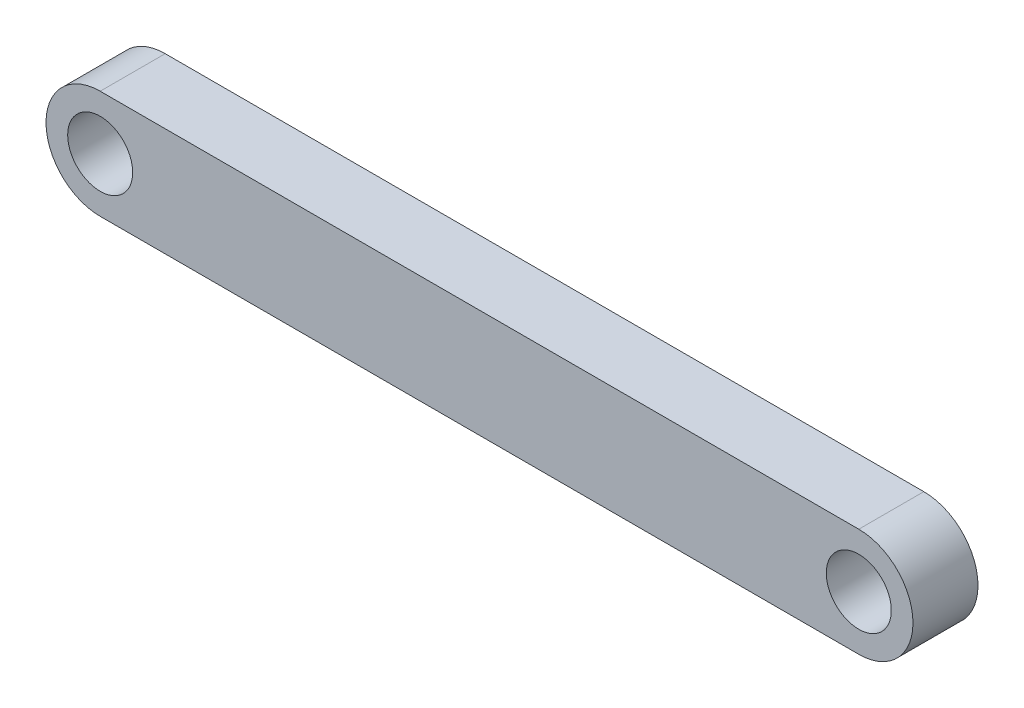
SolidWorks part; units mm, degrees
ref_plane "Ebene vorne" through (0, 0, 0) normal (0, 0, 1) x (1, 0, 0)
ref_plane "Ebene oben" through (0, 0, 0) normal (0, 1, 0) x (1, 0, 0)
ref_plane "Ebene rechts" through (0, 0, 0) normal (1, 0, 0) x (0, 0, -1)
sketch "Skizze1" plane through (0, 0, 0) normal (0, 0, 1) x (1, 0, 0)
  circle A0 centre (0, 670) radius 3.25
  circle A1 centre (70, 670) radius 3.25
sketch "Skizze2" plane through (0, 0, 0) normal (0, 0, 1) x (1, 0, 0)
  line L0 (0, 675) -> (70, 675)
  line L1 (0, 665) -> (70, 665)
  arc A0 (0, 675) -> (0, 665) centre (0, 670) ccw
  arc A1 (70, 665) -> (70, 675) centre (70, 670) ccw
  circle A2 centre (0, 670) radius 3
  circle A3 centre (70, 670) radius 3
  dimension "D1" = 10
extrude "Aufsatz-Linear austragen1" add sketch "Skizze2" along normal blind 6 from surface at 3
